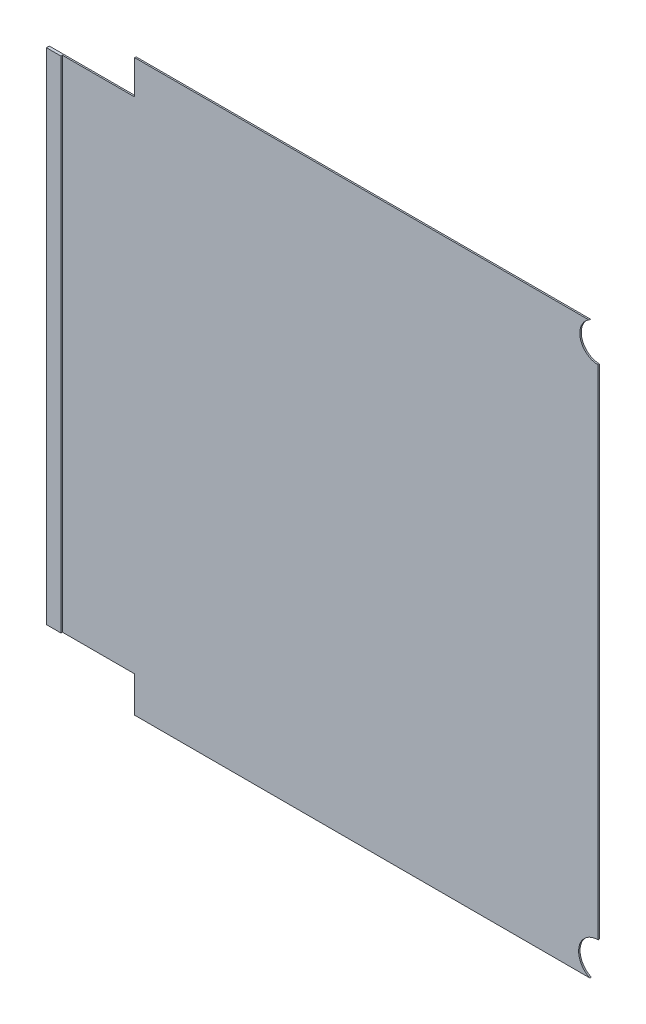
SolidWorks part; units mm, degrees
material "Thornel Mat VMA"
ref_plane "Płaszczyzna przednia" through (0, 0, 0) normal (0, 0, 1) x (1, 0, 0)
ref_plane "Płaszczyzna górna" through (0, 0, 0) normal (0, 1, 0) x (1, 0, 0)
ref_plane "Płaszczyzna prawa" through (0, 0, 0) normal (1, 0, 0) x (0, 0, -1)
sketch "Szkic1" plane through (0, 0, 0) normal (0, 0, 1) x (1, 0, 0)
  line L1 (-286.2786, 196) -> (-599.968, 196)
  line L2 (-280, 172.3343) -> (-280, -171.5174)
  line L3 (-285.747, -197.1963) -> (-599.968, -197.1963)
  line L4 (-649.968, 172.5) -> (-649.968, -172.5)
  line L7 (-649.968, 172.5) -> (-599.968, 172.5)
  line L8 (-599.968, 196) -> (-599.968, 172.5)
  line L12 (-649.968, -172.5) -> (-599.968, -172.5)
  line L13 (-599.968, -197.1963) -> (-599.968, -172.5)
  arc A2 (-280, -171.5174) -> (-285.747, -197.1963) centre (-280, -185) ccw
  arc A3 (-286.2786, 196) -> (-280, 172.3343) centre (-280, 185) ccw
  dimension "D1" = 50
  dimension "D2" = 50
extrude "Dodanie-wyciągnięcie1" add sketch "Szkic1" along normal blind 1
sketch "Szkic2" plane through (0, 0, 0) normal (0, 0, -1) x (-1, 0, 0)
  line L1 (649.968, 172.5) -> (659.968, 172.5)
  line L2 (649.968, 172.5) -> (649.968, -172.5)
  line L3 (649.968, -172.5) -> (659.968, -172.5)
  line L4 (659.968, 172.5) -> (659.968, -172.5)
  dimension "D1" = 10
extrude "Dodanie-wyciągnięcie2" add sketch "Szkic2" against normal blind 2
